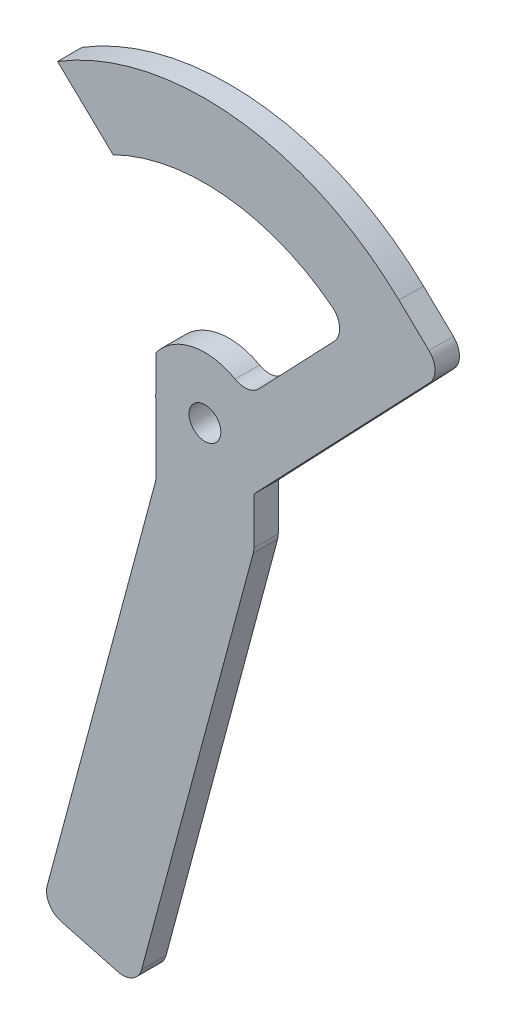
SolidWorks part; units mm, degrees
ref_plane "Front Plane" through (0, 0, 0) normal (0, 0, 1) x (1, 0, 0)
ref_plane "Top Plane" through (0, 0, 0) normal (0, 1, 0) x (1, 0, 0)
ref_plane "Right Plane" through (0, 0, 0) normal (1, 0, 0) x (0, 0, -1)
sketch "Model" plane through (0, 0, 0) normal (0, 0, 1) x (1, 0, 0)
  line L0 (344.4105, 264.2194) -> (350.5311, 258.3791)
  line L1 (350.6636, 252.7238) -> (314.4201, 214.7414)
  line L2 (315.7663, 234.2009) -> (331.15, 250.3227)
  line L3 (285.9358, 260.7455) -> (274.5744, 271.5868)
  line L4 (314.7153, 205.5132) -> (314.7153, 233.6197)
  line L5 (291.7754, 119.3737) -> (314.579, 204.478)
  line L6 (294.579, 207.111) -> (272.4569, 124.5501)
  line L7 (294.7153, 233.6197) -> (294.7153, 208.1463)
  line L8 (310.7153, 237.6197) -> (298.7153, 237.6197)
  line L9 (275.2853, 119.6511) -> (286.8764, 116.5452)
  arc A0 (304.4851, 232.692) -> (302.5414, 230.0337) centre (304.5326, 230.6176) ccw
  arc A1 (302.5414, 230.0337) -> (304.58, 228.5431) centre (304.5326, 230.6176) ccw
  arc A2 (310.6386, 222.7619) -> (304.58, 228.5431) centre (304.7153, 222.6197) ccw
  arc A3 (310.6386, 222.7619) -> (312.2231, 220.7953) centre (312.713, 222.8116) ccw
  arc A4 (312.2231, 220.7953) -> (314.7874, 222.8614) centre (312.713, 222.8116) ccw
  arc A5 (314.7874, 222.8614) -> (304.4851, 232.692) centre (304.7153, 222.6197) ccw
  arc A6 (298.792, 222.4775) -> (297.2076, 224.444) centre (296.7176, 222.4277) ccw
  arc A7 (297.2076, 224.444) -> (294.6432, 222.3779) centre (296.7176, 222.4277) ccw
  arc A8 (294.6432, 222.3779) -> (304.9455, 212.5473) centre (304.7153, 222.6197) ccw
  arc A9 (304.9455, 212.5473) -> (306.8892, 215.2056) centre (304.8981, 214.6218) ccw
  arc A10 (306.8892, 215.2056) -> (304.8507, 216.6962) centre (304.8981, 214.6218) ccw
  arc A11 (298.792, 222.4775) -> (304.8507, 216.6962) centre (304.7153, 222.6197) ccw
  circle A12 centre (304.7153, 222.6197) radius 3.25
  arc A13 (350.6636, 252.7238) -> (350.5311, 258.3791) centre (347.7697, 255.4852) ccw
  arc A14 (310.895, 233.4853) -> (314.4201, 214.7414) centre (304.7153, 222.6197) ccw
  arc A15 (331.15, 250.3227) -> (330.7019, 256.2492) centre (328.2561, 253.0841) ccw
  arc A16 (330.7019, 256.2492) -> (285.9358, 260.7455) centre (304.7153, 222.6197) ccw
  arc A17 (344.4105, 264.2194) -> (274.5744, 271.5868) centre (304.7153, 222.6197) ccw
  arc A18 (310.895, 233.4853) -> (315.7663, 234.2009) centre (312.8724, 236.9623) ccw
  arc A19 (314.7153, 233.6197) -> (310.7153, 237.6197) centre (310.7153, 233.6197) ccw
  arc A20 (314.579, 204.478) -> (314.7153, 205.5132) centre (310.7153, 205.5132) ccw
  arc A21 (286.8764, 116.5452) -> (291.7754, 119.3737) centre (287.9117, 120.4089) ccw
  arc A22 (272.4569, 124.5501) -> (275.2853, 119.6511) centre (276.3206, 123.5148) ccw
  arc A23 (294.579, 207.111) -> (294.7153, 208.1463) centre (290.7153, 208.1463) ccw
  arc A24 (298.7153, 237.6197) -> (294.7153, 233.6197) centre (298.7153, 233.6197) ccw
  circle A25 centre (304.7153, 230.6197) radius 2.075
  circle A26 centre (304.7153, 214.6197) radius 2.075
extrude "Boss-Extrude1" add sketch "Model" along normal blind 5 contours A23 L6 A22 L9 A21 L5 A20 L4 L1 A14 L7 | A18 L4 A5 A4 L1 A13 L0 A17 L3 A16 A15 L2 | A18 A14 L7 A7 A6 A11 A10 A9 A8 L1 L4 A4 A3 A2 A1 A0 A5 A12 | A25 A2 A3 A4 L4 A5 | A25 | A25 A5 A0 A1 A2 | A26 A11 A6 A7 L7 A8 | A26 | A4 A5 L4
